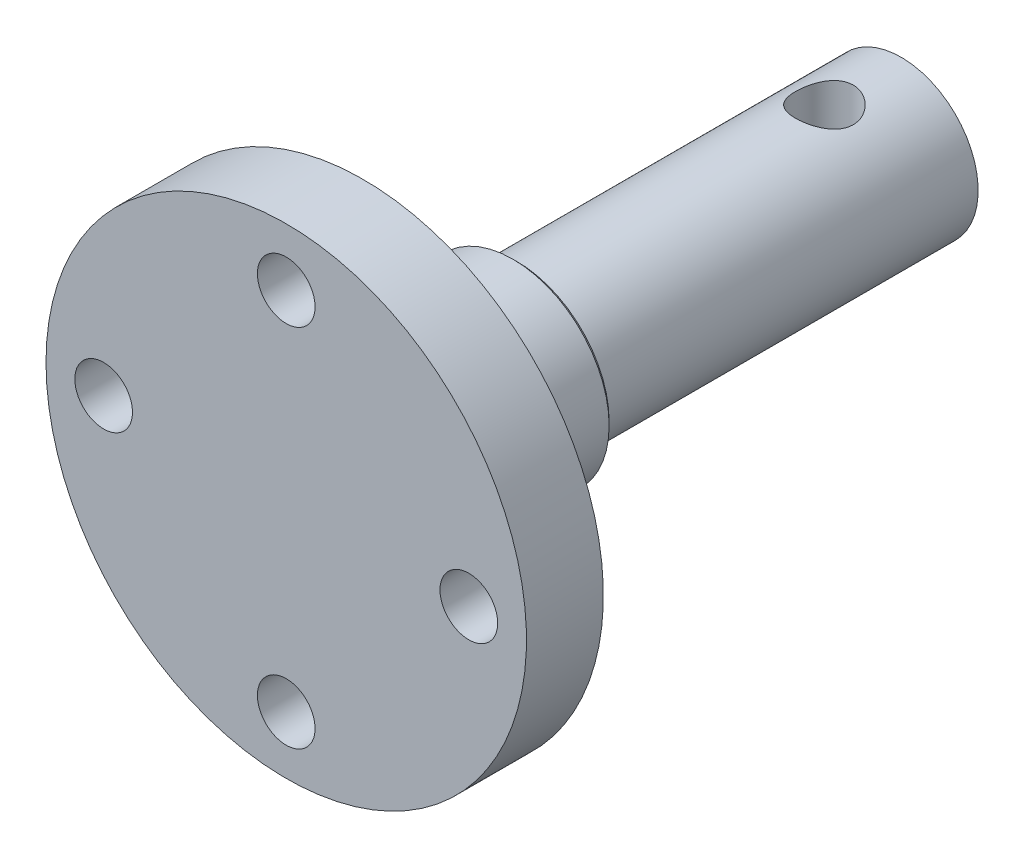
SolidWorks part; units mm, degrees
material "5052-H32"
ref_plane "Front Plane" through (0, 0, 0) normal (0, 0, 1) x (1, 0, 0)
ref_plane "Top Plane" through (0, 0, 0) normal (0, 1, 0) x (1, 0, 0)
ref_plane "Right Plane" through (0, 0, 0) normal (1, 0, 0) x (0, 0, -1)
sketch "Sketch1" plane through (0, 0, 0) normal (0, 1, 0) x (1, 0, 0)
  line L0 (0, 0) -> (0, -17.4703) construction
  line L1 (0, 0) -> (0, 32)
  line L2 (0, 32) -> (4, 32)
  line L3 (4, 32) -> (4, 12)
  line L4 (4, 12) -> (5, 12)
  line L5 (5, 12) -> (5, 4)
  line L6 (5, 4) -> (12.5, 4)
  line L7 (12.5, 4) -> (12.5, 0)
  line L8 (12.5, 0) -> (0, 0)
  line L9 (-4, 32) -> (-4, 12) construction
  line L10 (-5, 12) -> (-5, 4) construction
  line L11 (-12.5, 4) -> (-12.5, 0) construction
  line L12 (0, 24) -> (4, 24) construction
  dimension "D1" = 8
  dimension "D2" = 10
  dimension "D3" = 4
  dimension "D4" = 25
  dimension "D5" = 8
  dimension "D6" = 12
  dimension "D7" = 8
revolve "Revolve1" add sketch "Sketch1" angle 360 about L0
sketch "Sketch7" plane through (0, 0, -4) normal (0, 0, -1) x (-1, 0, 0)
  line L1 (0, 9.5) -> (-9.5, 0) construction
  line L2 (0, 9.5) -> (9.5, 0) construction
  line L3 (9.5, 0) -> (0, -9.5) construction
  line L4 (-9.5, 0) -> (0, -9.5) construction
  line L5 (0, 9.5) -> (0, -9.5) construction
  line L6 (9.5, 0) -> (-9.5, 0) construction
  circle A0 centre (0, 0) radius 9.5 construction
  circle A1 centre (-9.5, 0) radius 1.5
  circle A2 centre (0, 9.5) radius 1.5
  circle A3 centre (9.5, 0) radius 1.5
  circle A4 centre (0, -9.5) radius 1.5
  dimension "D1" = 19
  dimension "D2" = 3
sketch "Sketch4" plane through (0, 0, 0) normal (0, 1, 0) x (1, 0, 0)
  line L0 (0, 24) -> (0, 32) construction
  circle A0 centre (0, 28) radius 1.5
  dimension "D1" = 3
extrude "Cut-Extrude1" cut sketch "Sketch7" against normal through all
chamfer "Chamfer1" distance 0.2 angle 45 1 edges at (-5, 0, -12)
extrude "Cut-Extrude2" cut sketch "Sketch4" against normal through all both and the other way through all
